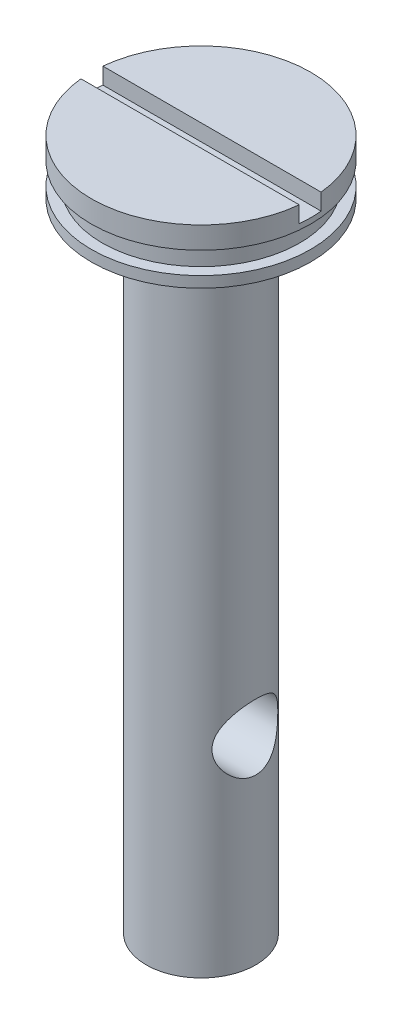
SolidWorks part; units mm, degrees
material "Rostfreier Chromstahl"
ref_plane "Ebene vorne" through (0, 0, 0) normal (0, 0, 1) x (1, 0, 0)
ref_plane "Ebene oben" through (0, 0, 0) normal (0, 1, 0) x (1, 0, 0)
ref_plane "Ebene rechts" through (0, 0, 0) normal (1, 0, 0) x (0, 0, -1)
sketch "Skizze1" plane through (0, 0, 0) normal (1, 0, 0) x (0, 0, -1)
  line L0 (10, 43) -> (10, 45)
  line L1 (0, 45) -> (0, -18)
  line L2 (0, -18) -> (5, -18)
  line L3 (5, -18) -> (5, 40)
  line L4 (5, 40) -> (10, 40)
  line L5 (10, 40) -> (10, 41)
  line L6 (10, 43) -> (9, 43)
  line L8 (0, -18) -> (0, -30) construction
  line L10 (10, 41) -> (9, 41)
  line L13 (10, 45) -> (0, 45)
  line L15 (0, 0) -> (5, 0) construction
  line L16 (9, 43) -> (9, 41)
  dimension "D1" = 10
  dimension "D2" = 5
  dimension "D3" = 18
  dimension "D4" = 20
  dimension "D5" = 40
  dimension "D6" = 1
  dimension "D7" = 2
  dimension "D8" = 1
revolve "Rotation1" add sketch "Skizze1" angle 360 about L8
sketch "Skizze5" plane through (0, 0, 0) normal (1, 0, 0) x (0, 0, -1)
  line L1 (-1, 45) -> (1, 45)
  line L2 (-1, 45) -> (-1, 43.5)
  line L3 (-1, 43.5) -> (1, 43.5)
  line L4 (1, 45) -> (1, 43.5)
  point P7 (0, 0)
  dimension "D1" = 1.5
  dimension "D2" = 2
extrude "Schnitt-Linear austragen1" cut sketch "Skizze5" against normal through all both and the other way through all
hole_wizard "Ø6.0 (6) Durchmesser Bohrung1" positions "3D-Skizze1" profile "Skizze4" hole size "Ø6.0" standard "DIN" end condition through all
sketch3d "3D-Skizze1"
  point P0 (5, 0, 0)
sketch "Skizze4" plane through (5, 0, 0) normal (0, 1, 0) x (0, 0, -1)
  line L0 (0, 0) -> (0, 15)
  line L1 (0, 15) -> (3, 15)
  line L2 (3, 15) -> (3, 0)
  line L5 (3, 0) -> (0, 0)
  line L11 (0, -6.35) -> (0, 107.95) construction
  dimension "Bohrerdurchmesser" = 6
  dimension "Bohrungstiefe" = 15
